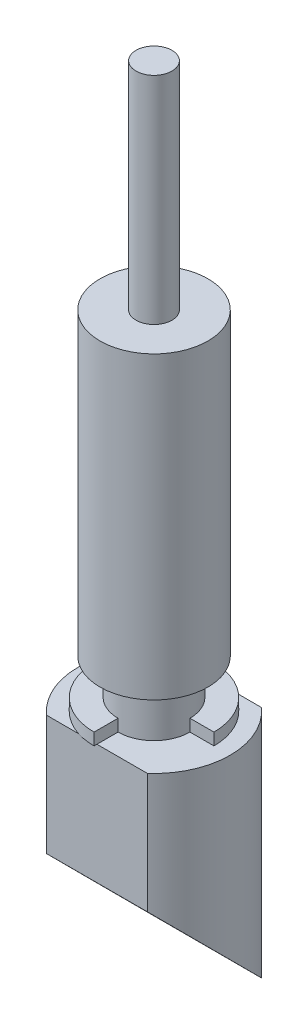
SolidWorks part; units mm, degrees
ref_plane "Front Plane" through (0, 0, 0) normal (0, 0, 1) x (1, 0, 0)
ref_plane "Top Plane" through (0, 0, 0) normal (0, 1, 0) x (1, 0, 0)
ref_plane "Right Plane" through (0, 0, 0) normal (1, 0, 0) x (0, 0, -1)
sketch "Sketch1" plane through (0, 0, 0) normal (0, 1, 0) x (1, 0, 0)
  circle A0 centre (0, 0) radius 4.5
  dimension "D1" = 9
extrude "Boss-Extrude1" add sketch "Sketch1" along normal blind 25
sketch "Sketch2" plane through (0, 0, 0) normal (0, -1, 0) x (1, 0, 0)
  circle A0 centre (0, 0) radius 3
  dimension "D1" = 6
extrude "Boss-Extrude2" add sketch "Sketch2" along normal blind 4
sketch "Sketch3" plane through (0, -4, 0) normal (0, -1, 0) x (1, 0, 0)
  line L0 (0, 3) -> (0, 5)
  line L1 (3, 0) -> (5, 0)
  arc A0 (0, 3) -> (3, 0) centre (0, 0) ccw
  arc A1 (0, 5) -> (5, 0) centre (0, 0) ccw
  circle A2 centre (0, 0) radius 5 construction
  circle A3 centre (0, 0) radius 3 construction
  dimension "D1" = 2
extrude "Boss-Extrude3" add sketch "Sketch3" against normal blind 1
sketch "Sketch4" plane through (0, -4, 0) normal (0, -1, 0) x (1, 0, 0)
  circle A0 centre (0, 0) radius 6.35
  dimension "D1" = 12.7
extrude "Boss-Extrude4" add sketch "Sketch4" along normal blind 19.54
sketch "Sketch5" plane through (0, -4, 0) normal (0, 1, 0) x (1, 0, 0)
  line L0 (0, 0) -> (6.35, 0) construction
  circle A0 centre (0, 0) radius 6.35 construction
ref_plane "Plane1" through (6.35, 0, 0) normal (1, 0, 0) x (0, 0, -1)
sketch "Sketch6" plane through (6.35, 0, 0) normal (1, 0, 0) x (0, 0, -1)
  line L0 (-8.9676, -4) -> (-4.76, -4)
  line L4 (4.76, -23.54) -> (-4.76, -14)
  line L5 (4.76, -4) -> (8.4598, -4)
  line L6 (-4.76, -14) -> (-4.76, -4)
  line L8 (4.76, -4) -> (4.76, -23.54)
  line L9 (8.4598, -4) -> (8.4598, -27.4767)
  line L10 (8.4598, -27.4767) -> (-8.9676, -27.4767)
  line L11 (-8.9676, -27.4767) -> (-8.9676, -4)
  dimension "D1" = 10
  dimension "D2" = 9.52
  dimension "D3" = 19.54
extrude "Cut-Extrude1" cut sketch "Sketch6" against normal blind 19.54
sketch "Sketch7" plane through (0, 25, 0) normal (0, 1, 0) x (1, 0, 0)
  circle A0 centre (0, 0) radius 1.5
  dimension "D1" = 3
extrude "Boss-Extrude5" add sketch "Sketch7" along normal blind 18
